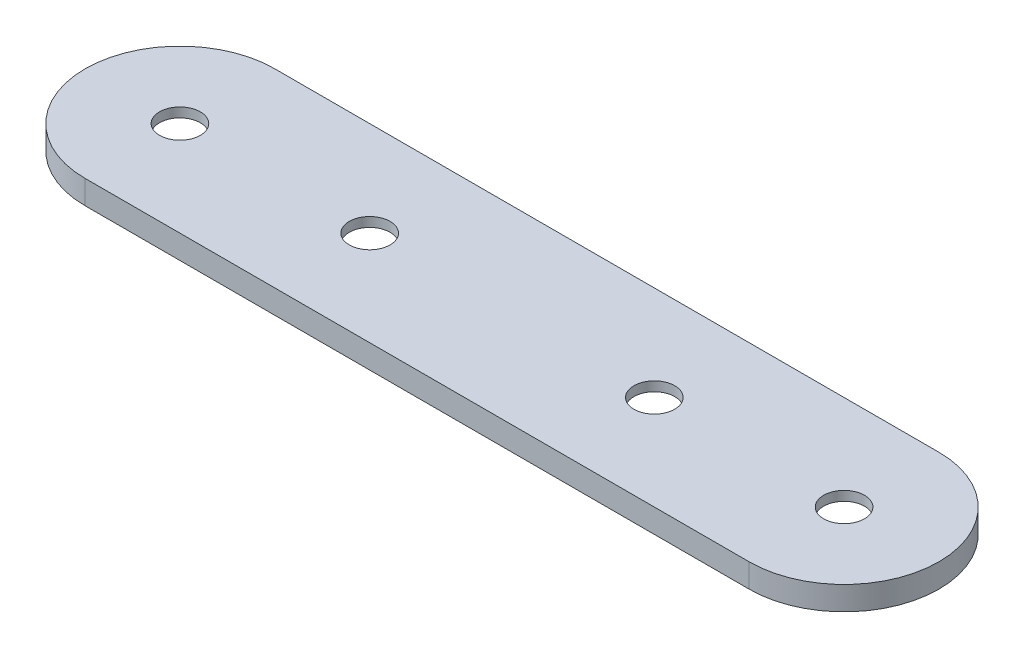
SolidWorks part; units mm, degrees
ref_plane "Front Plane" through (0, 0, 0) normal (0, 0, 1) x (1, 0, 0)
ref_plane "Top Plane" through (0, 0, 0) normal (0, 1, 0) x (1, 0, 0)
ref_plane "Right Plane" through (0, 0, 0) normal (1, 0, 0) x (0, 0, -1)
sketch "Sketch1" plane through (0, 0, 0) normal (0, 1, 0) x (1, 0, 0)
  line L0 (0, 0) -> (-70, 0) construction
  line L1 (0, -10) -> (-70, -10)
  line L2 (0, 10) -> (-70, 10)
  arc A0 (0, -10) -> (0, 10) centre (0, 0) ccw
  arc A1 (-70, 10) -> (-70, -10) centre (-70, 0) ccw
  circle A2 centre (0, 0) radius 2.15
  circle A3 centre (-70, 0) radius 2.15
  circle A4 centre (-20, 0) radius 2.15
  circle A5 centre (-50, 0) radius 2.15
  point P3 (-35, 0)
  dimension "D5" = 4.3
  dimension "D1" = 20
  dimension "D2" = 30
  dimension "D3" = 20
  dimension "D4" = 20
extrude "Boss-Extrude1" add sketch "Sketch1" against normal blind 2.5
chamfer "Chamfer1" distance 1.5 angle 60 4 edges at (-70, -2.5, 2.15) (-50, -2.5, 2.15) (-20, -2.5, 2.15) (0, -2.5, 2.15)
